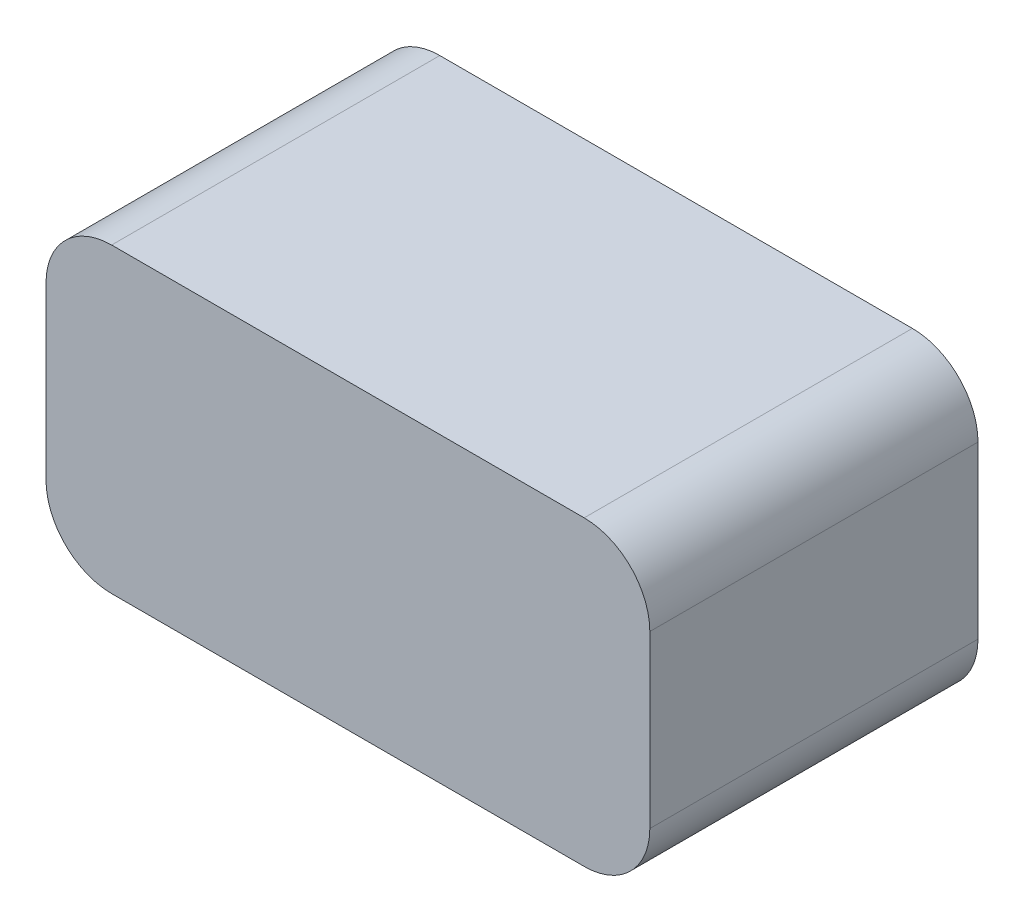
SolidWorks part; units mm, degrees
ref_plane "Front Plane" through (0, 0, 0) normal (0, 0, 1) x (1, 0, 0)
ref_plane "Top Plane" through (0, 0, 0) normal (0, 1, 0) x (1, 0, 0)
ref_plane "Right Plane" through (0, 0, 0) normal (1, 0, 0) x (0, 0, -1)
sketch "Sketch1" plane through (0, 0, 0) normal (0, 1, 0) x (1, 0, 0)
  line L1 (0, 0) -> (46, 0)
  line L2 (0, 0) -> (0, 25)
  line L3 (0, 25) -> (46, 25)
  line L4 (46, 0) -> (46, 25)
  dimension "D1" = 46
  dimension "D2" = 25
extrude "Boss-Extrude1" add sketch "Sketch1" along normal blind 23
fillet "Fillet1" radius 5 4 edges at (0, 0, -12.5) (0, 23, -12.5) (46, 0, -12.5) (46, 23, -12.5)
